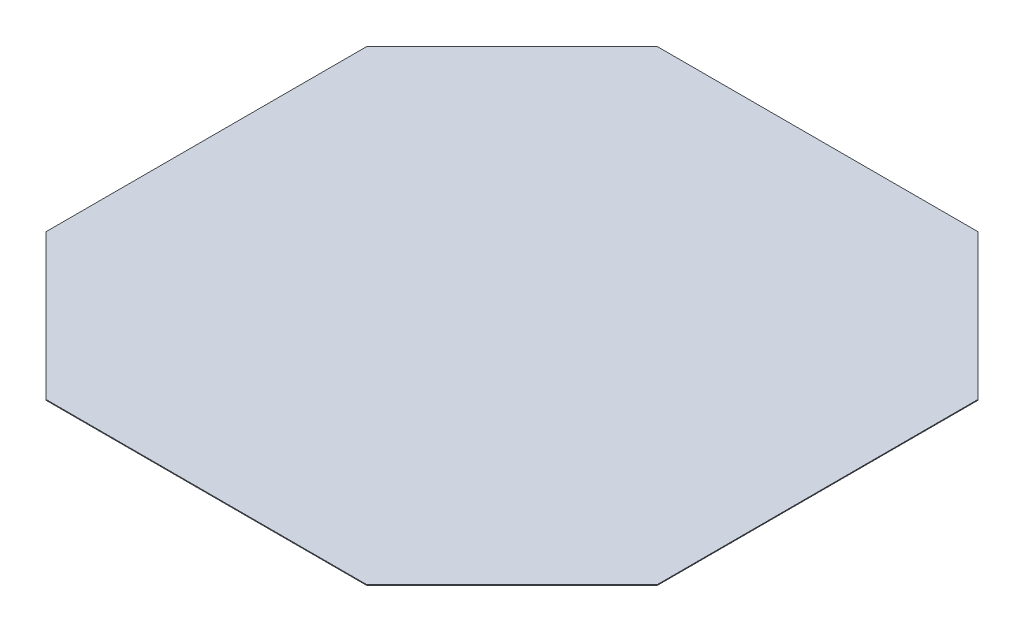
SolidWorks part; units mm, degrees
material "6061 Alloy"
ref_plane "Front Plane" through (0, 0, 0) normal (0, 0, 1) x (1, 0, 0)
ref_plane "Top Plane" through (0, 0, 0) normal (0, 1, 0) x (1, 0, 0)
ref_plane "Right Plane" through (0, 0, 0) normal (1, 0, 0) x (0, 0, -1)
sketch "Sketch1" plane through (0, 0, 0) normal (0, 1, 0) x (1, 0, 0)
  line L0 (-673.1, 1282.7) -> (-1282.7, 673.1)
  line L1 (-673.1, 1282.7) -> (673.1, 1282.7)
  line L2 (-1282.7, 673.1) -> (-1282.7, -673.1)
  line L3 (-673.1, -1282.7) -> (673.1, -1282.7)
  line L4 (1282.7, 673.1) -> (1282.7, -673.1)
  line L7 (673.1, 1282.7) -> (1282.7, 673.1)
  line L8 (673.1, -1282.7) -> (1282.7, -673.1)
  line L9 (-673.1, -1282.7) -> (-1282.7, -673.1)
  dimension "D1" = 609.6
  dimension "D2" = 609.6
  dimension "D3" = 1282.7
  dimension "D4" = 1282.7
  dimension "D5" = 609.6
  dimension "D6" = 609.6
  dimension "D7" = 609.6
  dimension "D8" = 609.6
  dimension "D9" = 609.6
  dimension "D10" = 609.6
  dimension "D11" = 2565.4
  dimension "D12" = 2565.4
extrude "Extrude1" add sketch "Sketch1" along normal blind 3.175
